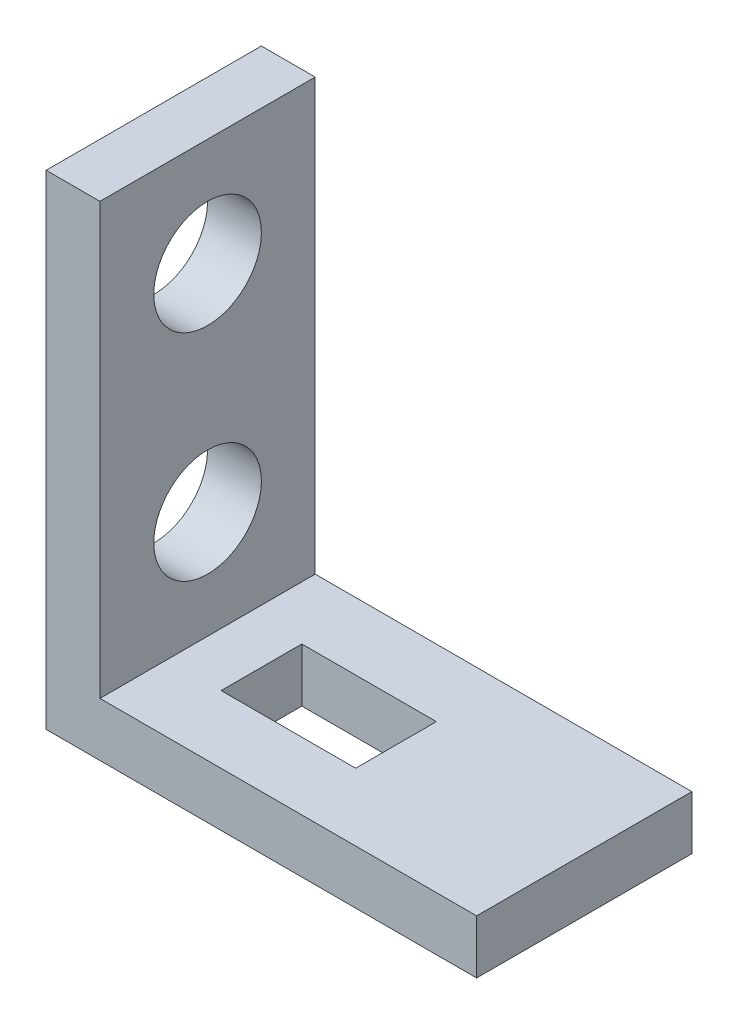
SolidWorks part; units mm, degrees
ref_plane "Front Plane" through (0, 0, 0) normal (0, 0, 1) x (1, 0, 0)
ref_plane "Top Plane" through (0, 0, 0) normal (0, 1, 0) x (1, 0, 0)
ref_plane "Right Plane" through (0, 0, 0) normal (1, 0, 0) x (0, 0, -1)
sketch "Sketch1" plane through (0, 0, 0) normal (0, 0, 1) x (1, 0, 0)
  line L1 (0, 0) -> (25.4, 0)
  line L2 (0, 0) -> (0, 28.575)
  line L3 (0, 28.575) -> (3.175, 28.575)
  line L4 (25.4, 0) -> (25.4, 3.175)
  line L7 (25.4, 3.175) -> (3.175, 3.175)
  line L8 (3.175, 28.575) -> (3.175, 3.175)
  dimension "D1" = 28.575
  dimension "D2" = 25.4
  dimension "D3" = 3.175
  dimension "D4" = 3.175
extrude "Boss-Extrude1" add sketch "Sketch1" along normal blind 12.7
sketch "Sketch2" plane through (3.175, 0, 0) normal (1, 0, 0) x (0, 0, -1)
  line L0 (-12.7, 3.175) -> (-12.7, 28.575) construction
  circle A0 centre (-6.35, 22.225) radius 3.175
  circle A2 centre (-6.35, 9.525) radius 3.175
  dimension "D5" = 6.35
  dimension "D1" = 12.7
  dimension "D3" = 6.35
extrude "Cut-Extrude1" cut sketch "Sketch2" against normal through all
sketch "Sketch4" plane through (0, 3.175, 0) normal (0, 1, 0) x (1, 0, 0)
  line L0 (25.4, -6.35) -> (3.0493, -6.35) construction
  line L1 (6.35, -8.7249) -> (14.2875, -8.7249)
  line L2 (6.35, -8.7249) -> (6.35, -3.9624)
  line L3 (6.35, -3.9624) -> (14.2875, -3.9624)
  line L4 (14.2875, -8.7249) -> (14.2875, -3.9624)
  line L9 (25.4, -12.7) -> (25.4, 0) construction
  line L10 (3.175, -12.7) -> (3.175, 0) construction
  dimension "D1" = 4.7625
  dimension "D2" = 7.9375
  dimension "D3" = 2.3876
  dimension "D5" = 3.175
extrude "Cut-Extrude2" cut sketch "Sketch4" against normal through all
